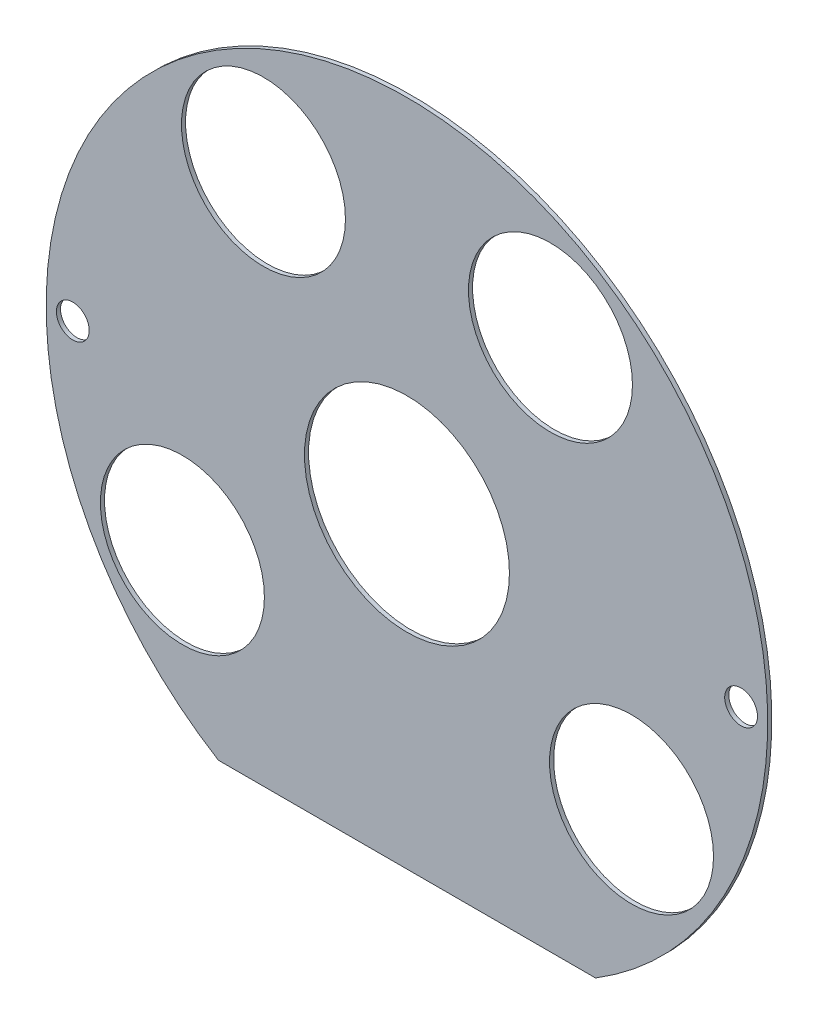
SolidWorks part; units mm, degrees
ref_plane "Plano frontal" through (0, 0, 0) normal (0, 0, 1) x (1, 0, 0)
ref_plane "Plano superior" through (0, 0, 0) normal (0, 1, 0) x (1, 0, 0)
ref_plane "Plano direito" through (0, 0, 0) normal (1, 0, 0) x (0, 0, -1)
sketch "Esboço1" plane through (0, 0, 0) normal (0, 0, 1) x (1, 0, 0)
  line L0 (-46, -75.02) -> (46, -75.02)
  line L1 (0, 0) -> (0, -75.02) construction
  line L2 (-54.772, -35) -> (0, -35) construction
  line L3 (0, -35) -> (54.772, -35) construction
  line L4 (0, -35) -> (0, 0) construction
  line L5 (0, 0) -> (0, 50000) construction
  line L6 (-35, 54.772) -> (0, 54.772) construction
  line L7 (0, 54.772) -> (35, 54.772) construction
  arc A0 (46, -75.02) -> (-46, -75.02) centre (0, 0) ccw
  circle A1 centre (0, 0) radius 25
  circle A2 centre (-35, 54.772) radius 20
  circle A3 centre (35, 54.772) radius 20
  circle A4 centre (-54.772, -35) radius 20
  circle A5 centre (54.772, -35) radius 20
  dimension "D1" = 176
  dimension "D3" = 50
  dimension "D4" = 40
  dimension "D2" = 92
  dimension "D5" = 35
  dimension "D6" = 54.772
  dimension "D7" = 35
  dimension "D8" = 54.772
extrude "Ressalto-extrusão1" add sketch "Esboço1" along normal blind 1
sketch "Esboço2" plane through (0, 0, 1) normal (0, 0, 1) x (1, 0, 0)
  circle A0 centre (-81.5, 0) radius 1.5 construction
  circle A1 centre (81.5, 0) radius 1.5 construction
  circle A2 centre (-81.5, 0) radius 1.5 construction
  circle A3 centre (81.5, 0) radius 1.5 construction
  circle A4 centre (81.5, 0) radius 4
  circle A5 centre (-81.5, 0) radius 4
  dimension "D1" = 8
extrude "Corte-extrusão1" cut sketch "Esboço2" against normal blind 1
